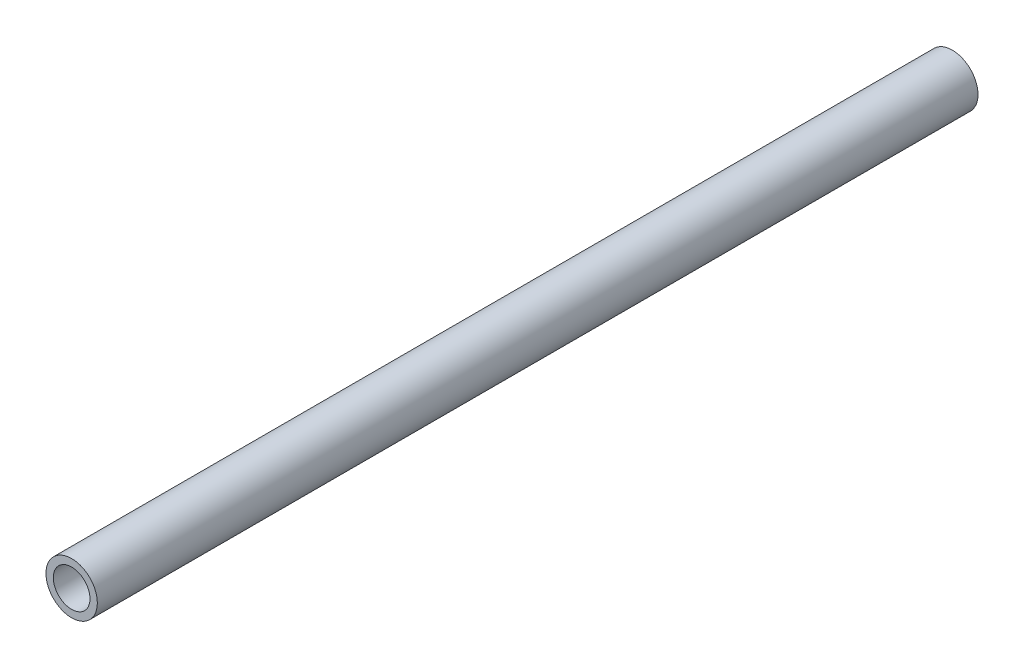
SolidWorks part; units mm, degrees
material "PVC Rigid"
ref_plane "Front Plane" through (0, 0, 0) normal (0, 0, 1) x (1, 0, 0)
ref_plane "Top Plane" through (0, 0, 0) normal (0, 1, 0) x (1, 0, 0)
ref_plane "Right Plane" through (0, 0, 0) normal (1, 0, 0) x (0, 0, -1)
sketch "Sketch1" plane through (0, 0, 0) normal (0, 0, 1) x (1, 0, 0)
  circle A0 centre (0, 0) radius 13.335
  dimension "D1" = 26.67
extrude "Boss-Extrude1" add sketch "Sketch1" along normal blind 457.2
sketch "Sketch2" plane through (0, 0, 0) normal (0, 0, -1) x (-1, 0, 0)
  circle A0 centre (0, 0) radius 9.525
  dimension "D1" = 19.05
extrude "Cut-Extrude1" cut sketch "Sketch2" against normal through all
equation "\"1foot\"=0.1"
